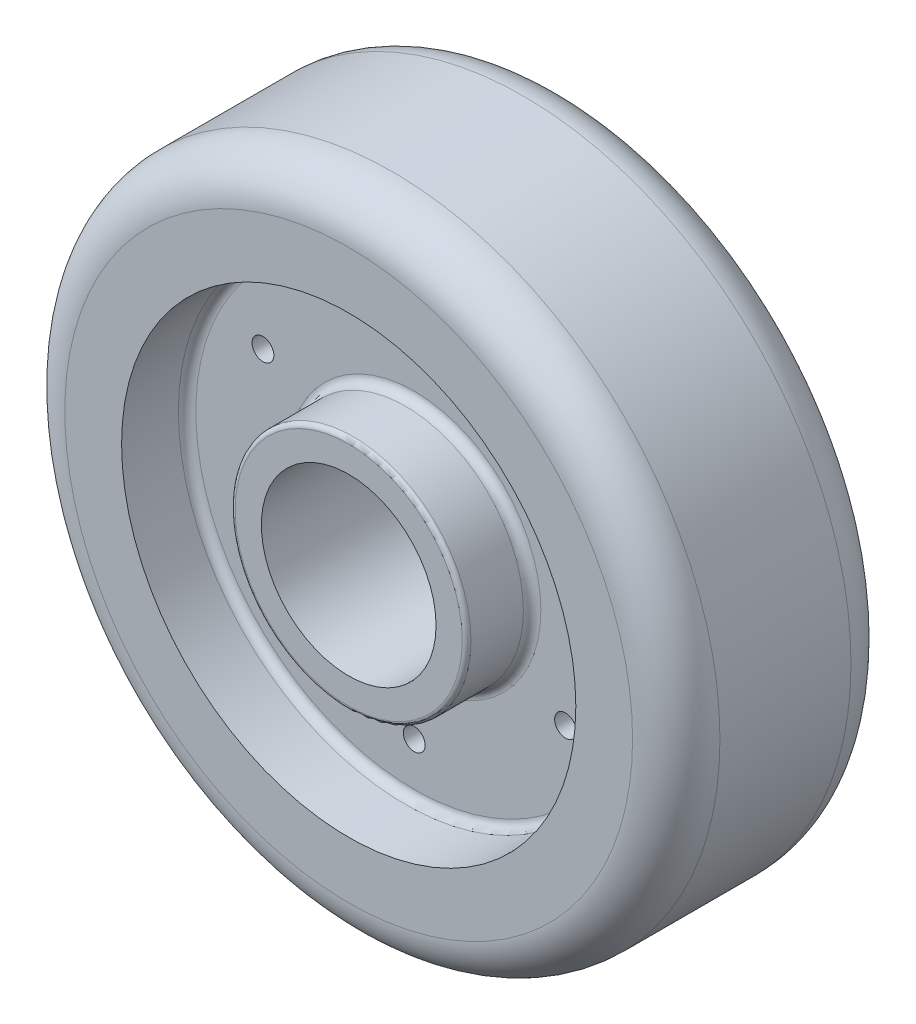
SolidWorks part; units mm, degrees
ref_plane "Front Plane" through (0, 0, 0) normal (0, 0, 1) x (1, 0, 0)
ref_plane "Top Plane" through (0, 0, 0) normal (0, 1, 0) x (1, 0, 0)
ref_plane "Right Plane" through (0, 0, 0) normal (1, 0, 0) x (0, 0, -1)
sketch "Sketch1" plane through (0, 0, 0) normal (0, 0, 1) x (1, 0, 0)
  circle A0 centre (0, 0) radius 75
  dimension "D1" = 150
extrude "Boss-Extrude1" add sketch "Sketch1" along normal mid plane 50
sketch "Sketch2" plane through (0, 0, 25) normal (0, 0, 1) x (1, 0, 0)
  circle A0 centre (0, 0) radius 52
  dimension "D1" = 104
extrude "Cut-Extrude1" cut sketch "Sketch2" against normal blind 15
sketch "Sketch3" plane through (0, 0, -25) normal (0, 0, -1) x (-1, 0, 0)
  circle A0 centre (0, 0) radius 52
  dimension "D1" = 104
extrude "Cut-Extrude2" cut sketch "Sketch3" against normal blind 15
sketch "Sketch4" plane through (0, 0, 10) normal (0, 0, 1) x (1, 0, 0)
  circle A0 centre (0, 0) radius 20
  circle A1 centre (0, 0) radius 27
  dimension "D1" = 40
  dimension "D2" = 54
extrude "Boss-Extrude2" add sketch "Sketch4" along normal blind 15
fillet "Fillet1" radius 10 2 edges at (75, 0, -25) (75, 0, 25)
fillet "Fillet2" radius 2 1 edges at (52, 0, 10)
fillet "Fillet3" radius 2 1 edges at (27, 0, 10)
fillet "Fillet4" radius 1 1 edges at (27, 0, 25)
ref_plane "Plane1" through (0, 0, 0) normal (0, 0, 1) x (1, 0, 0)
mirror "Mirror1" about plane through (0, 0, 0) normal (0, 0, 1) of "Boss-Extrude2"
fillet "Fillet5" radius 2 2 edges at (-52, 0, -10) (-27, 0, -10)
fillet "Fillet6" radius 1 1 edges at (27, 0, -25)
sketch "Sketch7" plane through (0, 0, 10) normal (0, 0, 1) x (1, 0, 0)
  circle A0 centre (0, 0) radius 20 construction
  circle A1 centre (0, 0) radius 20
extrude "Cut-Extrude3" cut sketch "Sketch7" against normal through all
sketch "Sketch8" plane through (0, 0, 10) normal (0, 0, 1) x (1, 0, 0)
  line L0 (0, 0) -> (0, 50) construction
  circle A0 centre (0, 0) radius 50 construction
  circle A1 centre (0, 40) radius 2.5
  circle A2 centre (34.641, 20) radius 2.5
  circle A3 centre (34.641, -20) radius 2.5
  circle A4 centre (0, -40) radius 2.5
  circle A5 centre (-34.641, -20) radius 2.5
  circle A6 centre (-34.641, 20) radius 2.5
  point P20 (0, 0)
  dimension "D1" = 5
  dimension "D2" = 40
  dimension "D3" = 6
extrude "Cut-Extrude4" cut sketch "Sketch8" against normal through all
